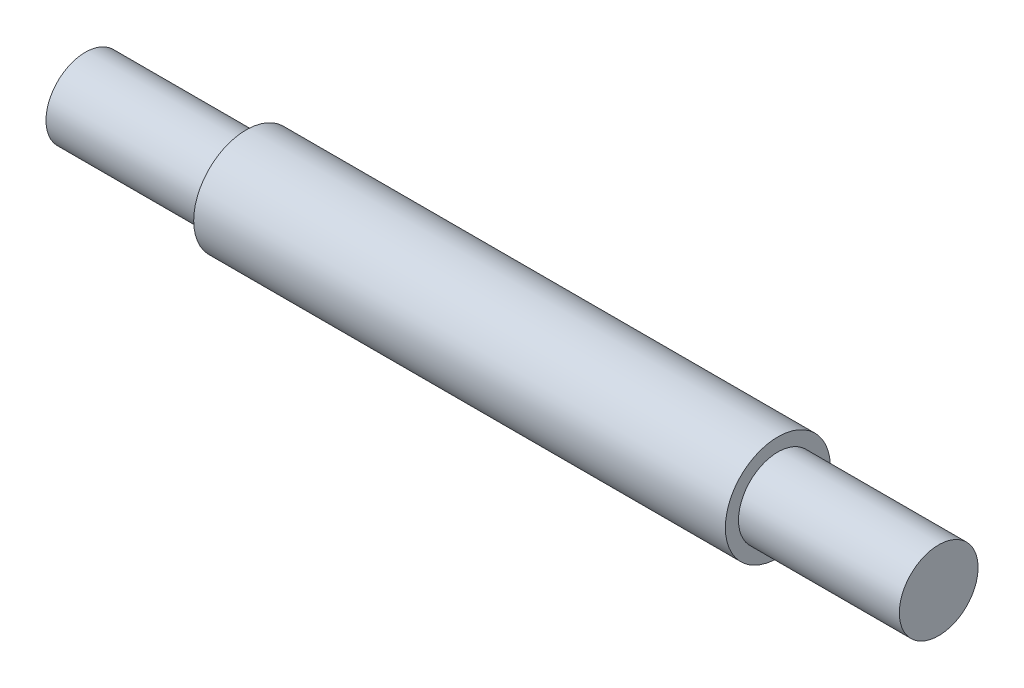
SolidWorks part; units mm, degrees
ref_plane "Front Plane" through (0, 0, 0) normal (0, 0, 1) x (1, 0, 0)
ref_plane "Top Plane" through (0, 0, 0) normal (0, 1, 0) x (1, 0, 0)
ref_plane "Right Plane" through (0, 0, 0) normal (1, 0, 0) x (0, 0, -1)
sketch "Sketch1" plane through (0, 0, 0) normal (0, 0, 1) x (1, 0, 0)
  line L0 (0, 0) -> (0, 8)
  line L1 (0, 8) -> (-40.5, 8)
  line L2 (-40.5, 8) -> (-40.5, 6)
  line L3 (-40.5, 6) -> (-65, 6)
  line L4 (-65, 6) -> (-65, 0)
  line L5 (-65, 0) -> (0, 0)
  dimension "D1" = 8
  dimension "D2" = 6
  dimension "D3" = 40.5
  dimension "D4" = 65
revolve "Revolve1" add sketch "Sketch1" angle 360 about L5
mirror "Mirror1" about plane through (0, 0, 0) normal (-1, 0, 0) of "Revolve1"
